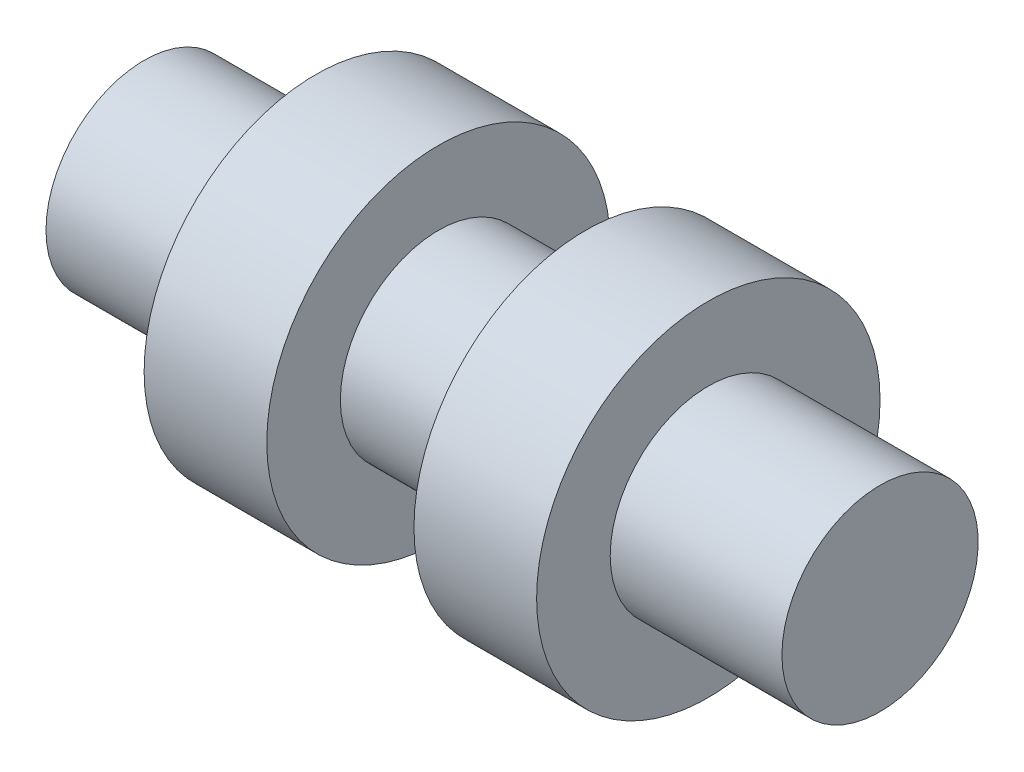
SolidWorks part; units mm, degrees
ref_plane "정면" through (0, 0, 0) normal (0, 0, 1) x (1, 0, 0)
ref_plane "윗면" through (0, 0, 0) normal (0, 1, 0) x (1, 0, 0)
ref_plane "우측면" through (0, 0, 0) normal (1, 0, 0) x (0, 0, -1)
sketch "스케치1" plane through (0, 0, 0) normal (0, 0, 1) x (1, 0, 0)
  line L0 (0, 0) -> (0, 20) construction
  line L1 (15, 20) -> (-15, 20)
  line L2 (-15, 20) -> (-15, 35)
  line L3 (15, 20) -> (15, 35)
  line L4 (-15, 35) -> (-40, 35)
  line L5 (15, 35) -> (40, 35)
  line L6 (-40, 35) -> (-40, 20)
  line L7 (40, 35) -> (40, 20)
  line L8 (-40, 20) -> (-75, 20)
  line L9 (40, 20) -> (75, 20)
  line L10 (-75, 20) -> (-75, 0)
  line L11 (75, 20) -> (75, 0)
  line L12 (-75, 0) -> (75, 0) construction
  line L13 (-75, 0) -> (0, 0)
  line L14 (0, 0) -> (75, 0)
  dimension "D1" = 30
  dimension "D2" = 80
  dimension "D3" = 150
  dimension "D4" = 40
  dimension "D5" = 70
revolve "회전1" add sketch "스케치1" angle 360 about L14
